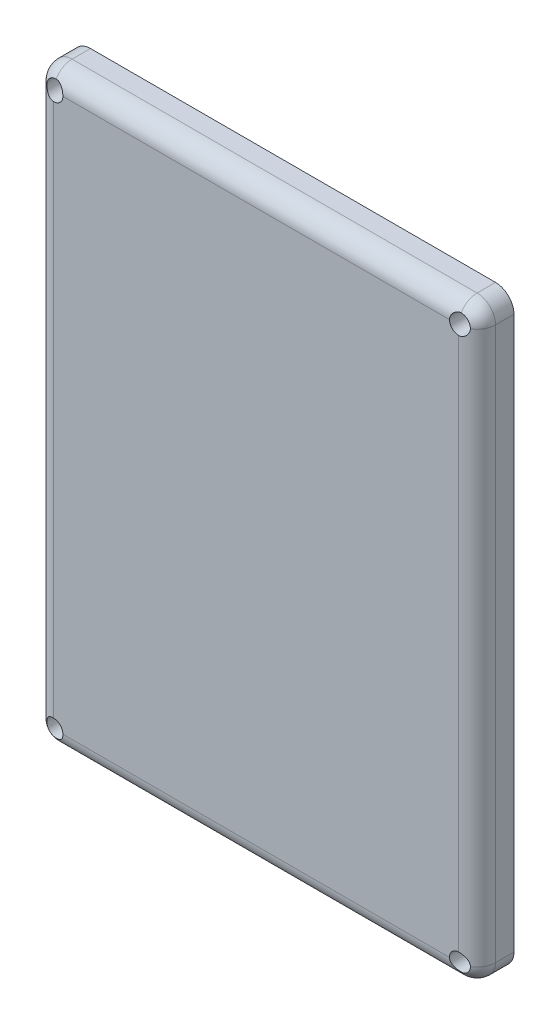
SolidWorks part; units mm, degrees
ref_plane "Front Plane" through (0, 0, 0) normal (0, 0, 1) x (1, 0, 0)
ref_plane "Top Plane" through (0, 0, 0) normal (0, 1, 0) x (1, 0, 0)
ref_plane "Right Plane" through (0, 0, 0) normal (1, 0, 0) x (0, 0, -1)
sketch "Sketch1" plane through (0, 0, 0) normal (0, 0, 1) x (1, 0, 0)
  line L6 (0, 0) -> (120, 0)
  line L7 (0, 0) -> (0, -160)
  line L8 (0, -160) -> (120, -160)
  line L9 (120, 0) -> (120, -160)
  dimension "D1" = 120
  dimension "D2" = 160
extrude "Boss-Extrude1" add sketch "Sketch1" along normal blind 10
sketch "Sketch2" plane through (0, 0, 0) normal (0, 0, -1) x (-1, 0, 0)
  line L0 (0, 0) -> (0, -160) construction
  line L1 (-110, -10) -> (-10, -10)
  line L2 (-110, -10) -> (-110, -150)
  line L3 (-110, -150) -> (-10, -150)
  line L4 (-10, -10) -> (-10, -150)
  line L5 (0, -160) -> (-120, -160) construction
  line L6 (-120, -160) -> (-120, 0) construction
  line L7 (-120, 0) -> (0, 0) construction
  dimension "D1" = 10
  dimension "D2" = 10
  dimension "D3" = 10
  dimension "D4" = 10
extrude "Cut-Extrude1" cut sketch "Sketch2" against normal blind 5
fillet "Fillet1" radius 5 1 edges at (10, -10, 2.5)
fillet "Fillet2" radius 5 3 edges at (110, -150, 2.5) (110, -10, 2.5) (10, -150, 2.5)
fillet "Fillet3" radius 5 8 edges at (60, 0, 10) (120, -80, 10) (60, -160, 10) (0, -80, 10) (120, 0, 5) (0, 0, 5) (0, -160, 5) (120, -160, 5)
sketch "Sketch3" plane through (0, 0, 10) normal (0, 0, 1) x (1, 0, 0)
  circle A0 centre (115, -5) radius 2.5
extrude "Cut-Extrude2" cut sketch "Sketch3" against normal blind 5
sketch "Sketch4" plane through (0, 0, 10) normal (0, 0, 1) x (1, 0, 0)
  circle A0 centre (5, -5) radius 2.5
extrude "Cut-Extrude3" cut sketch "Sketch4" against normal blind 5
sketch "Sketch5" plane through (0, 0, 10) normal (0, 0, 1) x (1, 0, 0)
  circle A0 centre (5, -155) radius 2.5
  circle A1 centre (115, -155) radius 2.5
extrude "Cut-Extrude4" cut sketch "Sketch5" against normal blind 5
sketch "Sketch6" plane through (0, 0, 5) normal (0, 0, 1) x (1, 0, 0)
  circle A0 centre (5, -5) radius 1.5
  circle A1 centre (115, -5) radius 1.5
  circle A2 centre (115, -155) radius 1.5
  circle A3 centre (5, -155) radius 1.5
extrude "Cut-Extrude5" cut sketch "Sketch6" against normal blind 10
